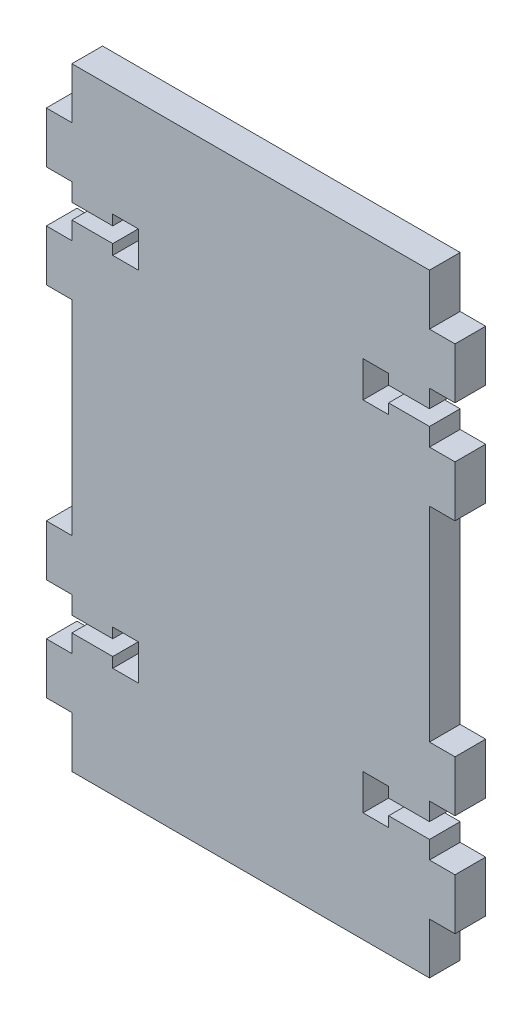
SolidWorks part; units mm, degrees
material "Cedro"
ref_plane "Plano frontal" through (0, 0, 0) normal (0, 0, 1) x (1, 0, 0)
ref_plane "Plano superior" through (0, 0, 0) normal (0, 1, 0) x (1, 0, 0)
ref_plane "Plano direito" through (0, 0, 0) normal (1, 0, 0) x (0, 0, -1)
sketch "Model" plane through (0, 0, 0) normal (0, 0, 1) x (1, 0, 0)
  line L0 (0, -10) -> (0, 0)
  line L1 (0, 0) -> (-70, 0)
  line L2 (-70, 0) -> (-70, -10)
  line L3 (-70, -10) -> (-75, -10)
  line L4 (-75, -10) -> (-75, -20)
  line L5 (-75, -20) -> (-70, -20)
  line L6 (-70, -20) -> (-70, -23.5)
  line L7 (-70, -23.5) -> (-62, -23.5)
  line L8 (-62, -23.5) -> (-62, -21.5)
  line L9 (-62, -21.5) -> (-57, -21.5)
  line L10 (-57, -21.5) -> (-57, -28.5)
  line L11 (-57, -28.5) -> (-62, -28.5)
  line L12 (-62, -28.5) -> (-62, -26.5)
  line L13 (-62, -26.5) -> (-70, -26.5)
  line L14 (-70, -26.5) -> (-70, -30)
  line L15 (-70, -30) -> (-75, -30)
  line L16 (-75, -30) -> (-75, -40)
  line L17 (-75, -40) -> (-70, -40)
  line L18 (-70, -40) -> (-70, -80)
  line L19 (-70, -80) -> (-75, -80)
  line L20 (-75, -80) -> (-75, -90)
  line L21 (-75, -90) -> (-70, -90)
  line L22 (-70, -90) -> (-70, -93.5)
  line L23 (-70, -93.5) -> (-62, -93.5)
  line L24 (-62, -93.5) -> (-62, -91.5)
  line L25 (-62, -91.5) -> (-57, -91.5)
  line L26 (-57, -91.5) -> (-57, -98.5)
  line L27 (-57, -98.5) -> (-62, -98.5)
  line L28 (-62, -98.5) -> (-62, -96.5)
  line L29 (-62, -96.5) -> (-70, -96.5)
  line L30 (-70, -96.5) -> (-70, -100)
  line L31 (-70, -100) -> (-75, -100)
  line L32 (-75, -100) -> (-75, -110)
  line L33 (-75, -110) -> (-70, -110)
  line L34 (-70, -110) -> (-70, -120)
  line L35 (-70, -120) -> (0, -120)
  line L36 (0, -120) -> (0, -110)
  line L37 (0, -110) -> (5, -110)
  line L38 (5, -110) -> (5, -100)
  line L39 (5, -100) -> (0, -100)
  line L40 (0, -100) -> (0, -96.5)
  line L41 (0, -96.5) -> (-8, -96.5)
  line L42 (-8, -96.5) -> (-8, -98.5)
  line L43 (-8, -98.5) -> (-13, -98.5)
  line L44 (-13, -98.5) -> (-13, -91.5)
  line L45 (-13, -91.5) -> (-8, -91.5)
  line L46 (-8, -91.5) -> (-8, -93.5)
  line L47 (-8, -93.5) -> (0, -93.5)
  line L48 (0, -93.5) -> (0, -90)
  line L49 (0, -90) -> (5, -90)
  line L50 (5, -90) -> (5, -80)
  line L51 (5, -80) -> (0, -80)
  line L52 (0, -80) -> (0, -40)
  line L53 (0, -40) -> (5, -40)
  line L54 (5, -40) -> (5, -30)
  line L55 (5, -30) -> (0, -30)
  line L56 (0, -30) -> (0, -26.5)
  line L57 (0, -26.5) -> (-8, -26.5)
  line L58 (-8, -26.5) -> (-8, -28.5)
  line L59 (-8, -28.5) -> (-13, -28.5)
  line L60 (-13, -28.5) -> (-13, -21.5)
  line L61 (-13, -21.5) -> (-8, -21.5)
  line L62 (-8, -21.5) -> (-8, -23.5)
  line L63 (-8, -23.5) -> (0, -23.5)
  line L64 (0, -23.5) -> (0, -20)
  line L65 (0, -20) -> (5, -20)
  line L66 (5, -20) -> (5, -10)
  line L67 (5, -10) -> (0, -10)
extrude "Ressalto-extrusão1" add sketch "Model" along normal blind 6
